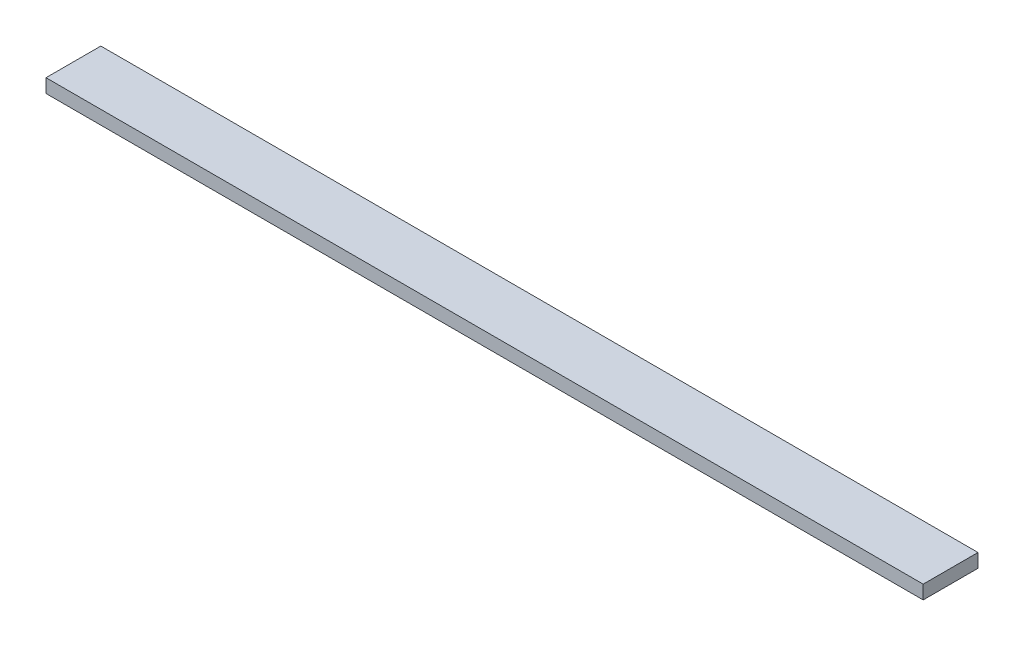
SolidWorks part; units mm, degrees
ref_plane "Front Plane" through (0, 0, 0) normal (0, 0, 1) x (1, 0, 0)
ref_plane "Top Plane" through (0, 0, 0) normal (0, 1, 0) x (1, 0, 0)
ref_plane "Right Plane" through (0, 0, 0) normal (1, 0, 0) x (0, 0, -1)
sketch "Sketch1" plane through (0, 0, 0) normal (1, 0, 0) x (0, 0, -1)
  line L1 (0, 0) -> (1, 0)
  line L2 (0, 0) -> (0, 0.25)
  line L3 (0, 0.25) -> (1, 0.25)
  line L4 (1, 0) -> (1, 0.25)
  dimension "D1" = 0.25
  dimension "D2" = 1
extrude "Boss-Extrude1" add sketch "Sketch1" along normal blind 16
scale "Scale1" scale about centroid uniform scaling yes scale factor 25.4
